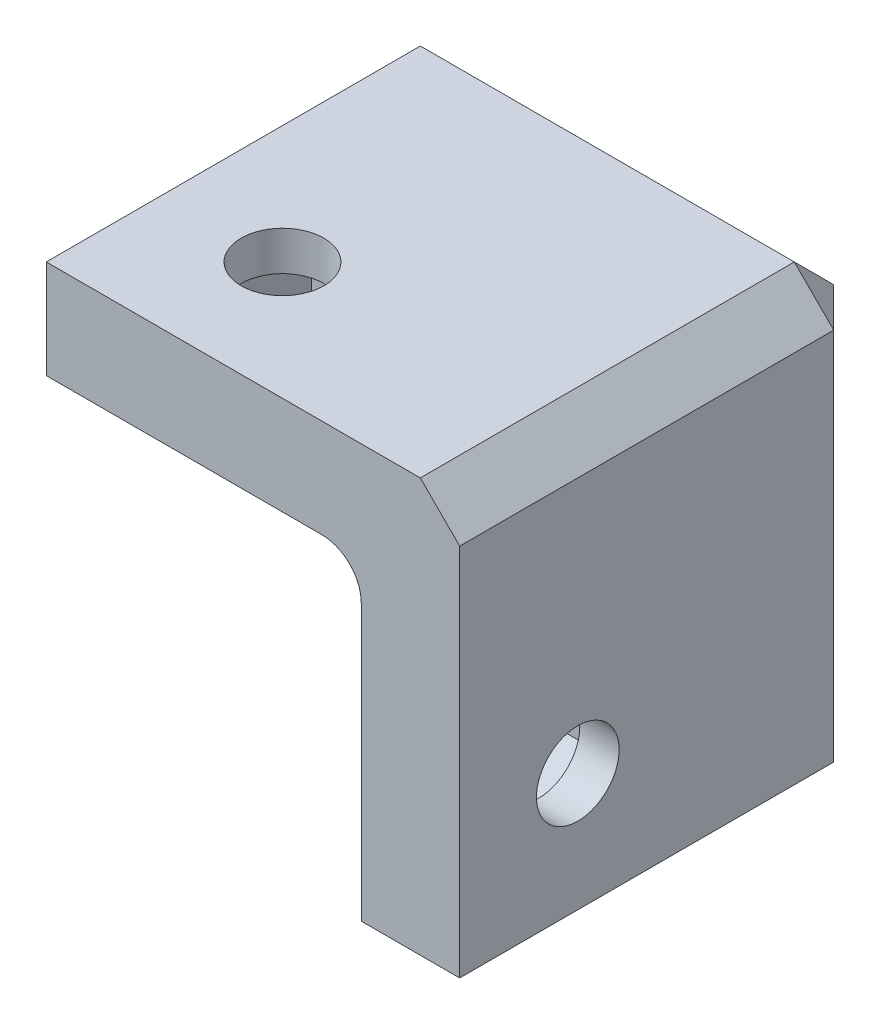
SolidWorks part; units mm, degrees
ref_plane "Front Plane" through (0, 0, 0) normal (0, 0, 1) x (1, 0, 0)
ref_plane "Top Plane" through (0, 0, 0) normal (0, 1, 0) x (1, 0, 0)
ref_plane "Right Plane" through (0, 0, 0) normal (1, 0, 0) x (0, 0, -1)
sketch "Sketch1" plane through (0, 0, 0) normal (0, 0, 1) x (1, 0, 0)
  line L1 (0, 0) -> (21, 0)
  line L2 (0, 0) -> (0, 21)
  line L3 (0, 21) -> (21, 21)
  line L4 (21, 0) -> (21, 21)
  dimension "D1" = 21
  dimension "D2" = 21
extrude "Boss-Extrude1" add sketch "Sketch1" along normal blind 5
sketch "Sketch2" plane through (0, 0, 5) normal (0, 0, 1) x (1, 0, 0)
  line L0 (21, 0) -> (21, 21) construction
  line L1 (0, 21) -> (21, 21)
  line L2 (0, 21) -> (0, 16)
  line L3 (0, 16) -> (16, 16)
  line L5 (0, 0) -> (21, 0) construction
  line L7 (21, 21) -> (21, 0)
  line L8 (21, 0) -> (16, 0)
  line L9 (16, 16) -> (16, 0)
  dimension "D1" = 5
  dimension "D2" = 5
extrude "Boss-Extrude2" add sketch "Sketch2" along normal blind 16
sketch "Sketch3" plane through (0, 21, 0) normal (0, 1, 0) x (1, 0, 0)
  line L0 (21, -21) -> (21, 0) construction
  line L1 (21, 0) -> (0, 0) construction
  circle A0 centre (6, -15) radius 2.1
  dimension "D1" = 4.2
  dimension "D2" = 15
  dimension "D3" = 15
extrude "Cut-Extrude1" cut sketch "Sketch3" against normal blind 3
sketch "Sketch4" plane through (21, 0, 0) normal (1, 0, 0) x (0, 0, -1)
  line L0 (0, 0) -> (0, 21) construction
  line L1 (-21, 21) -> (0, 21) construction
  circle A0 centre (-15, 6) radius 2.1
  dimension "D1" = 4.2
  dimension "D2" = 15
  dimension "D3" = 15
extrude "Cut-Extrude2" cut sketch "Sketch4" against normal blind 3
sketch "Sketch5" plane through (0, 0, 0) normal (0, 0, -1) x (-1, 0, 0)
  line L0 (-21, 21) -> (0, 21) construction
  line L1 (-21, 0) -> (-21, 21) construction
  circle A0 centre (-6, 6) radius 2.1
  dimension "D1" = 4.2
  dimension "D2" = 15
  dimension "D3" = 15
extrude "Cut-Extrude3" cut sketch "Sketch5" against normal blind 3
sketch "Sketch6" plane through (16, 0, 0) normal (-1, 0, 0) x (0, 0, 1)
  line L0 (21, 21) -> (0, 21) construction
  line L1 (18.5, 3.9793) -> (18.5, 8.0207)
  line L2 (18.5, 8.0207) -> (15, 10.0415)
  line L3 (15, 10.0415) -> (11.5, 8.0207)
  line L4 (11.5, 8.0207) -> (11.5, 3.9793)
  line L5 (11.5, 3.9793) -> (15, 1.9585)
  line L6 (15, 1.9585) -> (18.5, 3.9793)
  line L7 (0, 21) -> (0, 0) construction
  circle A0 centre (15, 6) radius 3.5 construction
  dimension "D2" = 15
  dimension "D3" = 15
  dimension "D1" = 7
extrude "Cut-Extrude4" cut sketch "Sketch6" against normal blind 3
sketch "Sketch7" plane through (0, 0, 5) normal (0, 0, 1) x (1, 0, 0)
  line L0 (21, 21) -> (0, 21) construction
  line L1 (9.5, 3.9793) -> (9.5, 8.0207)
  line L2 (9.5, 8.0207) -> (6, 10.0415)
  line L3 (6, 10.0415) -> (2.5, 8.0207)
  line L4 (2.5, 8.0207) -> (2.5, 3.9793)
  line L5 (2.5, 3.9793) -> (6, 1.9585)
  line L6 (6, 1.9585) -> (9.5, 3.9793)
  line L8 (21, 0) -> (21, 21) construction
  circle A0 centre (6, 6) radius 3.5 construction
  dimension "D1" = 7
  dimension "D3" = 15
  dimension "D2" = 15
extrude "Cut-Extrude5" cut sketch "Sketch7" against normal blind 3
sketch "Sketch8" plane through (0, 16, 0) normal (0, -1, 0) x (1, 0, 0)
  line L0 (21, 21) -> (21, 0) construction
  line L1 (8.0207, 11.5) -> (10.0415, 15)
  line L2 (10.0415, 15) -> (8.0207, 18.5)
  line L3 (8.0207, 18.5) -> (3.9793, 18.5)
  line L4 (3.9793, 18.5) -> (1.9585, 15)
  line L5 (1.9585, 15) -> (3.9793, 11.5)
  line L6 (3.9793, 11.5) -> (8.0207, 11.5)
  line L7 (0, 0) -> (21, 0) construction
  circle A0 centre (6, 15) radius 3.5 construction
  dimension "D1" = 7
  dimension "D2" = 15
  dimension "D3" = 15
extrude "Cut-Extrude6" cut sketch "Sketch8" against normal blind 3
chamfer "Chamfer1" distance 2 angle 45 3 edges at (21, 21, 10.5) (10.5, 21, 0) (21, 10.5, 0)
fillet "Fillet1" radius 2 3 edges at (16, 16, 13)
